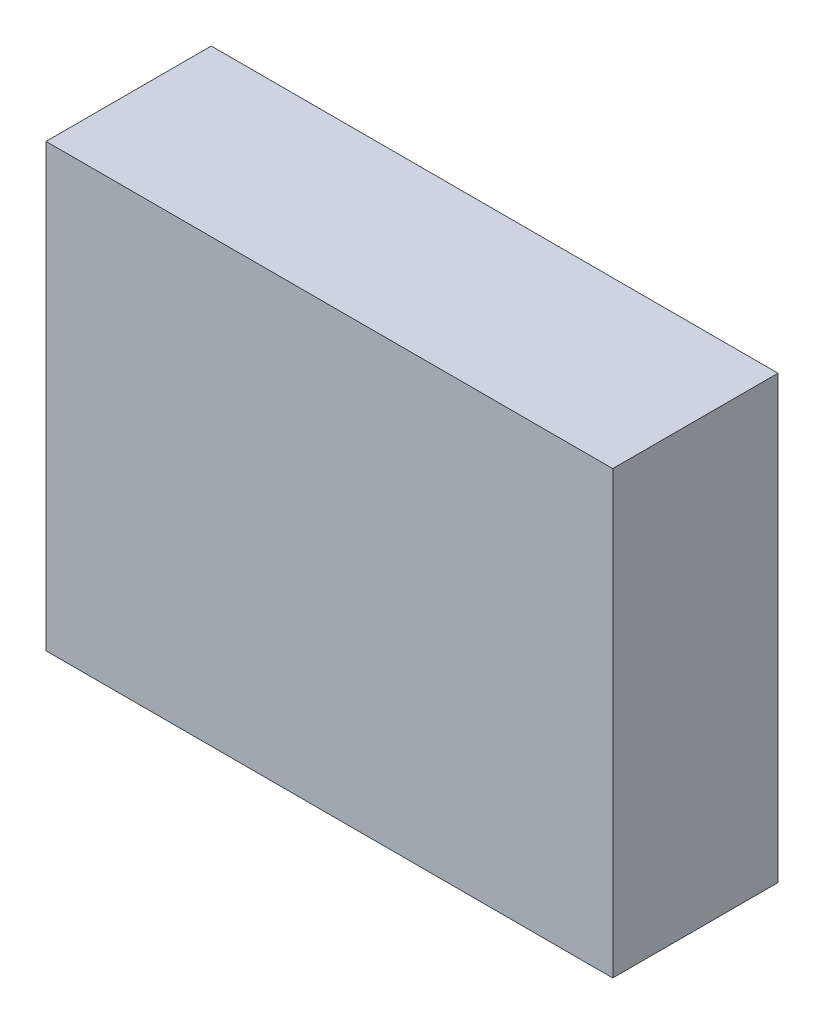
SolidWorks part; units mm, degrees
ref_plane "Front" through (0, 0, 0) normal (0, 0, 1) x (1, 0, 0)
ref_plane "Top" through (0, 0, 0) normal (0, 1, 0) x (1, 0, 0)
ref_plane "Right" through (0, 0, 0) normal (1, 0, 0) x (0, 0, -1)
sketch "Sketch1" plane through (0, 0, 0) normal (0, 0, 1) x (1, 0, 0)
  line L1 (-34.3, 26.7) -> (34.3, 26.7)
  line L2 (-34.3, 26.7) -> (-34.3, -26.7)
  line L3 (-34.3, -26.7) -> (34.3, -26.7)
  line L4 (34.3, 26.7) -> (34.3, -26.7)
  line L5 (-34.3, 26.7) -> (34.3, -26.7) construction
  line L6 (-34.3, -26.7) -> (34.3, 26.7) construction
  point P0 (0, 0)
  dimension "D1" = 68.6
  dimension "D2" = 53.4
extrude "Boss-Extrude1" add sketch "Sketch1" along normal blind 20
